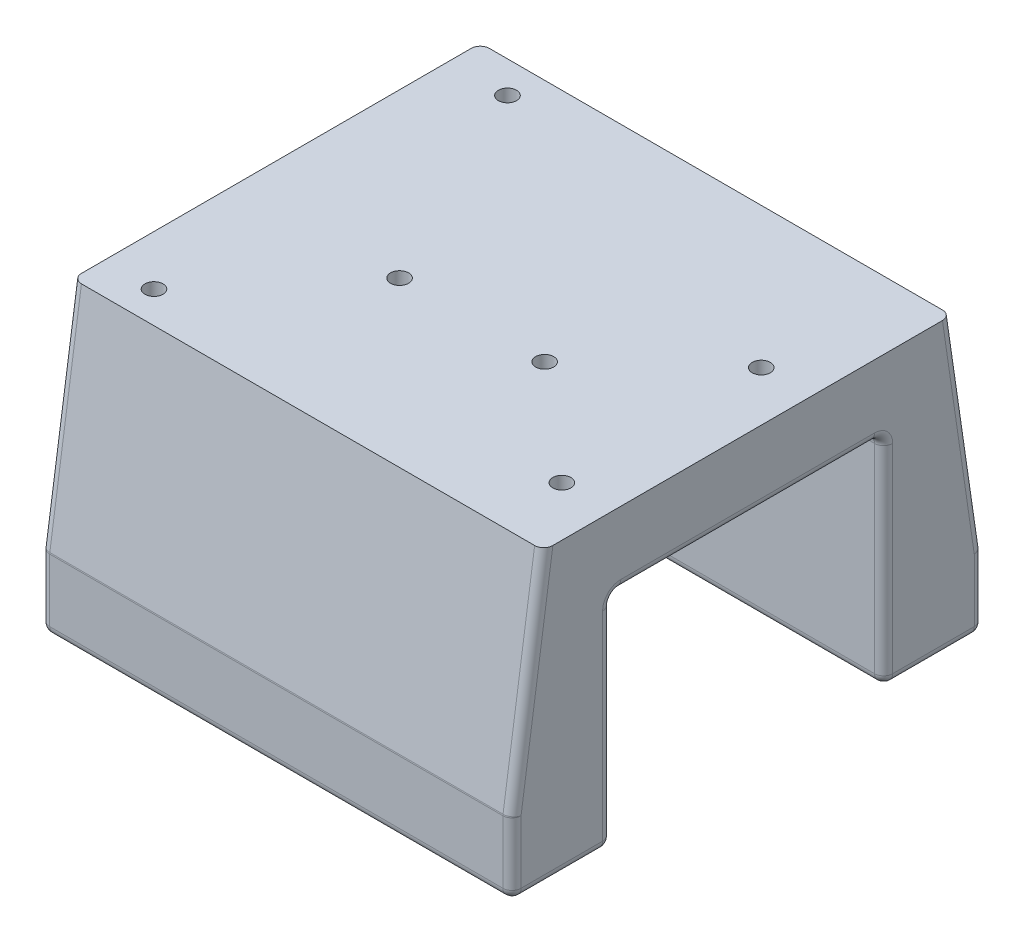
SolidWorks part; units mm, degrees
material "ABS"
ref_plane "Front Plane" through (0, 0, 0) normal (0, 0, 1) x (1, 0, 0)
ref_plane "Top Plane" through (0, 0, 0) normal (0, 1, 0) x (1, 0, 0)
ref_plane "Right Plane" through (0, 0, 0) normal (1, 0, 0) x (0, 0, -1)
sketch "Sketch1" plane through (0, 0, 0) normal (0, 0, 1) x (1, 0, 0)
  line L0 (0, 0) -> (66.04, 0)
  line L1 (66.04, 0) -> (66.04, 10.16)
  line L2 (66.04, 10.16) -> (0, 10.16)
  line L3 (0, 0) -> (0, 10.16)
  dimension "D2" = 10.16
  dimension "D3" = 66.04
extrude "Boss-Extrude1" add sketch "Sketch1" along normal blind 66.04 contours L0 L1 L2 L3
sketch "Sketch5" plane through (0, 10.16, 0) normal (0, 1, 0) x (1, 0, 0)
  line L0 (0, -66.04) -> (0, 0) construction
  line L1 (0, -61.595) -> (66.04, -61.595)
  line L2 (0, -61.595) -> (0, -4.445)
  line L3 (0, -4.445) -> (66.04, -4.445)
  line L4 (66.04, -61.595) -> (66.04, -4.445)
  line L5 (66.04, -66.04) -> (66.04, 0) construction
  line L6 (33.02, 0) -> (33.02, -4.445) construction
  line L7 (66.04, 0) -> (0, 0) construction
  line L8 (33.02, -61.595) -> (33.02, -66.04) construction
  line L9 (66.04, -66.04) -> (0, -66.04) construction
  dimension "D1" = 57.15
extrude "Boss-Extrude2" add sketch "Sketch5" along normal blind 30.48
sketch "Sketch6" plane through (0, 0, 0) normal (-1, 0, 0) x (0, 0, 1)
  line L0 (66.04, 0) -> (0, 0) construction
  line L1 (13.97, 0) -> (52.07, 0)
  line L2 (13.97, 0) -> (13.97, 30.48)
  line L3 (13.97, 30.48) -> (52.07, 30.48)
  line L4 (52.07, 0) -> (52.07, 30.48)
  line L5 (0, 0) -> (13.97, 0) construction
  line L6 (52.07, 0) -> (66.04, 0) construction
  dimension "D1" = 38.1
  dimension "D2" = 30.48
extrude "Cut-Extrude4" cut sketch "Sketch6" against normal through all contours L2 L3 L4 L1
sketch "Sketch7" plane through (0, 40.64, 0) normal (0, 1, 0) x (1, 0, 0)
  line L0 (0, -8.89) -> (66.04, -8.89) construction
  line L1 (0, -4.445) -> (0, -61.595) construction
  line L2 (66.04, -61.595) -> (66.04, -4.445) construction
  line L3 (0, -57.15) -> (66.04, -57.15) construction
  line L4 (33.02, -8.89) -> (33.02, -4.445) construction
  line L5 (66.04, -4.445) -> (0, -4.445) construction
  line L6 (33.02, -57.15) -> (33.02, -61.595) construction
  line L7 (0, -61.595) -> (66.04, -61.595) construction
  line L8 (6.985, -8.89) -> (6.985, -57.15) construction
  line L9 (59.055, -57.15) -> (59.055, -8.89) construction
  line L10 (59.055, -33.02) -> (66.04, -33.02) construction
  line L11 (6.985, -33.02) -> (0, -33.02) construction
  line L12 (59.055, -38.608) -> (6.985, -38.608) construction
  line L13 (33.02, -38.608) -> (33.02, -57.15) construction
  line L14 (43.18, -38.608) -> (22.86, -38.608) construction
  circle A0 centre (6.985, -57.15) radius 1.27
  circle A1 centre (8.255, -8.89) radius 1.27
  circle A2 centre (59.055, -24.13) radius 1.27
  circle A3 centre (59.055, -52.07) radius 1.27
  circle A4 centre (43.18, -38.608) radius 1.27
  circle A5 centre (22.86, -38.608) radius 1.27
  dimension "D6" = 2.54
  dimension "D1" = 48.26
  dimension "D2" = 52.07
  dimension "D3" = 1.27
  dimension "D4" = 15.24
  dimension "D5" = 5.08
  dimension "D7" = 5.588
  dimension "D8" = 20.32
extrude "Cut-Extrude5" cut sketch "Sketch7" against normal blind 7.62
sketch "Sketch8" plane through (66.04, 0, 0) normal (1, 0, 0) x (0, 0, -1)
  line L0 (-61.595, 10.16) -> (-66.04, 10.16)
  line L1 (-66.04, 10.16) -> (-61.595, 40.64)
  line L2 (-61.595, 40.64) -> (-61.595, 10.16)
  line L3 (-4.445, 10.16) -> (-4.445, 40.64)
  line L4 (-4.445, 40.64) -> (0, 10.16)
  line L5 (0, 10.16) -> (-4.445, 10.16)
extrude "Boss-Extrude3" add sketch "Sketch8" against normal up to surface (66.04 mm away) up to face at (0, 17.78, 33.3904)
fillet "Fillet1" radius 1.27 26 edges at (66.04, 15.24, 52.07) (66.04, 15.24, 13.97) (0, 15.24, 13.97) (0, 15.24, 52.07) (33.02, 30.48, 52.07) (66.04, 30.48, 33.02) (33.02, 30.48, 13.97) (0, 30.48, 33.02) (0, 5.08, 0) (66.04, 5.08, 0) (66.04, 5.08, 66.04) (0, 5.08, 66.04) (66.04, 0, 6.985) (0, 0, 6.985) (33.02, 0, 13.97) (33.02, 0, 0) (33.02, 10.16, 0) (33.02, 10.16, 66.04) (33.02, 0, 66.04) (66.04, 0, 59.055) (33.02, 0, 52.07) (0, 0, 59.055) (0, 25.4, 63.8175) (66.04, 25.4, 63.8175) (0, 25.4, 2.2225) (66.04, 25.4, 2.2225)
sketch "Sketch9" plane through (0, 0, 0) normal (0, -1, 0) x (1, 0, 0)
  line L0 (58.42, 58.42) -> (64.77, 58.42) construction
  line L4 (64.77, 53.34) -> (64.77, 64.77) construction
  line L5 (7.62, 58.42) -> (1.27, 58.42) construction
  line L6 (1.27, 64.77) -> (1.27, 53.34) construction
  line L7 (58.42, 58.42) -> (58.42, 64.77) construction
  line L8 (64.77, 64.77) -> (1.27, 64.77) construction
  line L9 (58.42, 7.62) -> (58.42, 1.27) construction
  line L10 (1.27, 1.27) -> (64.77, 1.27) construction
  circle A0 centre (58.42, 58.42) radius 2.54
  circle A1 centre (7.62, 58.42) radius 2.54
  circle A2 centre (7.62, 7.62) radius 2.54
  circle A3 centre (58.42, 7.62) radius 2.54
  dimension "D3" = 5.08
  dimension "D1" = 50.8
  dimension "D2" = 50.8
extrude "Cut-Extrude6" cut sketch "Sketch9" against normal blind 10.16
ref_plane "Plane1" through (0, 15.24, 0) normal (0, -1, 0) x (-1, 0, 0)
